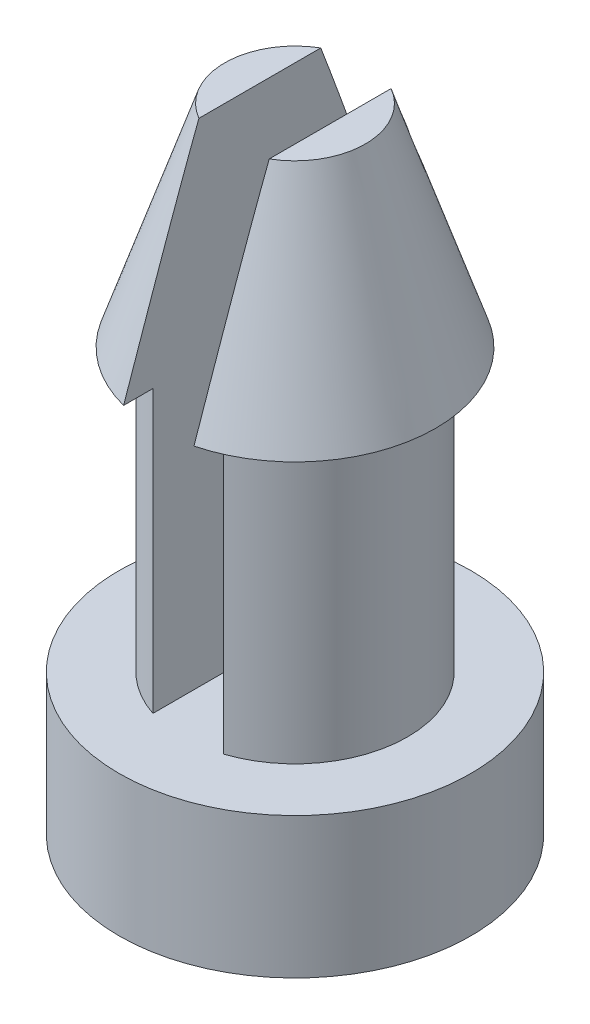
SolidWorks part; units mm, degrees
ref_plane "Front Plane" through (0, 0, 0) normal (0, 0, 1) x (1, 0, 0)
ref_plane "Top Plane" through (0, 0, 0) normal (0, 1, 0) x (1, 0, 0)
ref_plane "Right Plane" through (0, 0, 0) normal (1, 0, 0) x (0, 0, -1)
sketch "Sketch1" plane through (0, 0, 0) normal (1, 0, 0) x (0, 0, -1)
  line L0 (0, 0) -> (3.9688, 0)
  line L1 (0, 0) -> (0, 15.3293) construction
  line L2 (2.54, 3.175) -> (2.54, 9.525)
  line L3 (2.54, 9.525) -> (0, 9.525) construction
  line L4 (3.9688, 0) -> (3.9688, 3.175)
  line L5 (3.9688, 3.175) -> (0, 3.175)
  line L6 (0, 14.2875) -> (1.5875, 14.2875)
  line L7 (1.5875, 14.2875) -> (3.175, 9.525)
  line L8 (3.175, 9.525) -> (2.54, 9.525) construction
  line L9 (3.175, 9.525) -> (0, 9.525)
  line L10 (0, 14.2875) -> (0, 0)
  dimension "D1" = 7.9375
  dimension "D2" = 5.08
  dimension "D3" = 6.35
  dimension "D4" = 3.175
  dimension "D5" = 3.175
  dimension "D6" = 4.7625
  dimension "D7" = 6.35
revolve "Revolve1" add sketch "Sketch1" angle 360 about L1
sketch "Sketch2" plane through (0, 0, 0) normal (0, 0, 1) x (1, 0, 0)
  line L0 (1.5875, 14.2875) -> (-1.5875, 14.2875) construction
  line L1 (-0.7937, 14.2875) -> (0.7937, 14.2875)
  line L2 (-0.7937, 14.2875) -> (-0.7937, 3.175)
  line L3 (-0.7937, 3.175) -> (0.7937, 3.175)
  line L4 (0.7937, 14.2875) -> (0.7937, 3.175)
  line L5 (3.9688, 3.175) -> (-3.9688, 3.175) construction
  point P8 (0, 3.175)
  dimension "D1" = 1.5875
extrude "Cut-Extrude1" cut sketch "Sketch2" against normal through all both and the other way through all
